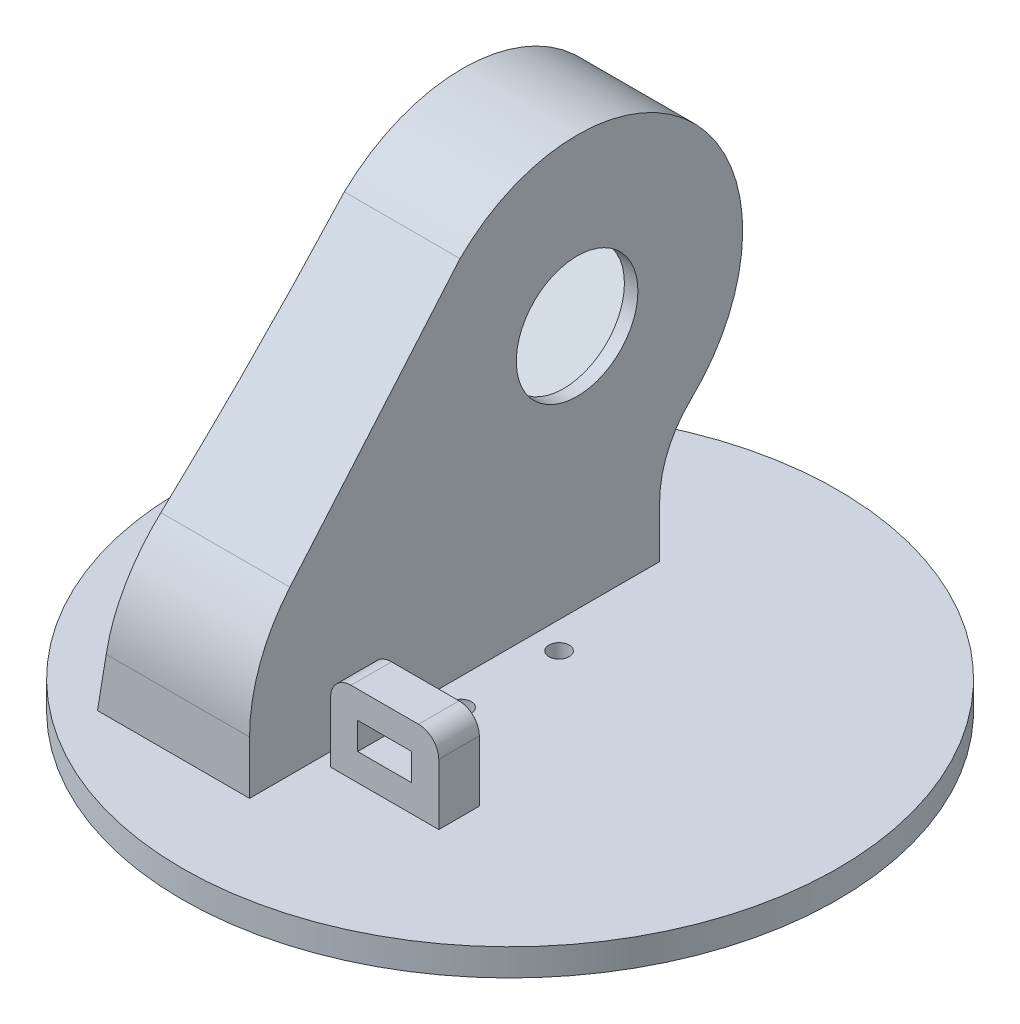
SolidWorks part; units mm, degrees
ref_plane "Front Plane" through (0, 0, 0) normal (0, 0, 1) x (1, 0, 0)
ref_plane "Top Plane" through (0, 0, 0) normal (0, 1, 0) x (1, 0, 0)
ref_plane "Right Plane" through (0, 0, 0) normal (1, 0, 0) x (0, 0, -1)
sketch "Sketch2" plane through (0, 0, 0) normal (0, 1, 0) x (1, 0, 0)
  circle A0 centre (0, 0) radius 48.5
  dimension "D1" = 97
extrude "Boss-Extrude1" add sketch "Sketch2" along normal blind 4
sketch "Sketch4" plane through (0, 0, 0) normal (0, -1, 0) x (1, 0, 0)
  circle A0 centre (0, 7.25) radius 1.5
  circle A1 centre (0, -7.25) radius 1.5
  dimension "D1" = 3
  dimension "D2" = 3
  dimension "D3" = 14.5
  dimension "D4" = 7.25
extrude "Cut-Extrude2" cut sketch "Sketch4" against normal through all
sketch "Sketch5" plane through (0, 0, 0) normal (0, -1, 0) x (1, 0, 0)
  circle A0 centre (0, 0) radius 3.75
  dimension "D1" = 7.5
extrude "Cut-Extrude3" cut sketch "Sketch5" against normal blind 1.5
ref_plane "Plane1" through (-4, 0, 0) normal (1, 0, 0) x (0, 0, -1)
sketch "Sketch7" plane through (-4, 0, 0) normal (1, 0, 0) x (0, 0, -1)
  line L0 (23.1299, 11.6445) -> (23.1299, 4)
  line L5 (48.5, 4) -> (-48.5, 4) construction
  line L6 (-27.2273, 29.5362) -> (-1.2843, 55.4793)
  line L7 (-43.5609, 4) -> (23.1299, 4)
  line L11 (-34.5496, 4) -> (-34.5496, 11.8586)
  arc A4 (28.7298, 24.692) -> (-1.2843, 55.4793) centre (13.9185, 40.2765) ccw
  arc A5 (28.7298, 24.692) -> (23.1299, 11.6445) centre (41.1299, 11.6445) ccw
  arc A6 (-27.2273, 29.5362) -> (-34.5496, 11.8586) centre (-9.5496, 11.8586) ccw
  dimension "D1" = 25
  dimension "D4" = 43
  dimension "D3" = 18
  dimension "D5" = 45
extrude "Boss-Extrude2" add sketch "Sketch7" against normal blind 14
ref_plane "Plane2" through (-6, 0, 0) normal (1, 0, 0) x (0, 0, -1)
sketch "Sketch8" plane through (-6, 0, 0) normal (1, 0, 0) x (0, 0, -1)
  line L0 (-27.2273, 29.5362) -> (-1.2843, 55.4793) construction
  line L1 (-15.2496, 25.9576) -> (13.7417, 54.9489)
  line L2 (-15.2496, 25.9576) -> (-0.4004, 11.1083)
  line L3 (-0.4004, 11.1083) -> (28.591, 40.0997)
  line L4 (13.7417, 54.9489) -> (28.591, 40.0997)
  line L5 (-15.2496, 25.9576) -> (28.591, 40.0997) construction
  line L6 (-0.4004, 11.1083) -> (13.7417, 54.9489) construction
  point P0 (6.6707, 33.0286)
  point P11 (13.9185, 40.2765)
  dimension "D1" = 41
  dimension "D2" = 21
  dimension "D3" = 90
  dimension "D4" = 20.5
  dimension "D5" = 90
  dimension "D6" = 10.25
  dimension "D7" = 10.5
extrude "Cut-Extrude5" cut sketch "Sketch8" against normal up to next
sketch "Sketch9" plane through (-18, 0, 0) normal (-1, 0, 0) x (0, 0, 1)
  line L0 (-13.7417, 54.9489) -> (-28.591, 40.0997) construction
  line L3 (-21.1664, 47.5243) -> (-22.536, 48.894) construction
  circle A0 centre (-20.1057, 53.5347) radius 1.3
  circle A1 centre (-27.1768, 46.4637) radius 1.3
  circle A2 centre (6.7644, 12.5225) radius 1.3
  circle A3 centre (13.8354, 19.5936) radius 1.3
  dimension "D1" = 2.6
  dimension "D5" = 5
  dimension "D6" = 90
  dimension "D2" = 3.5
  dimension "D3" = 2
  dimension "D4" = 2
extrude "Cut-Extrude6" cut sketch "Sketch9" against normal blind 7.5
sketch "Sketch11" plane through (-4, 0, 0) normal (1, 0, 0) x (0, 0, -1)
  circle A0 centre (13.9185, 40.2765) radius 9
  dimension "D1" = 18
extrude "Cut-Extrude9" cut sketch "Sketch11" against normal up to next
sketch "Sketch17" plane through (-18, 0, 0) normal (-1, 0, 0) x (0, 0, 1)
  line L0 (29.3486, 31.6576) -> (3.4056, 57.6006)
  line L1 (-26.1299, 11.6445) -> (-26.1299, 1)
  line L2 (-26.1299, 1) -> (37.5496, 1)
  line L3 (37.5496, 1) -> (37.5496, 11.8586)
  line L4 (27.2273, 29.5362) -> (1.2843, 55.4793)
  line L5 (-23.1299, 11.6445) -> (-23.1299, 4)
  line L6 (-23.1299, 4) -> (34.5496, 4)
  line L7 (34.5496, 4) -> (34.5496, 11.8586)
  line L9 (-23.1299, 11.6445) -> (-23.1299, 4)
  line L10 (-23.1299, 4) -> (34.5496, 4)
  line L11 (34.5496, 4) -> (34.5496, 11.8586)
  line L12 (-26.1299, 4) -> (37.5496, 4)
  line L13 (48.5, 4) -> (-48.5, 4) construction
  line L14 (3.4056, 57.6006) -> (28.5745, 28.0776)
  line L15 (1.2843, 55.4793) -> (26.295, 26.1272)
  line L16 (31.5496, 11.8586) -> (31.5496, 4)
  line L18 (27.2273, 29.5362) -> (1.2843, 55.4793) construction
  arc A0 (3.4056, 57.6006) -> (-30.7965, 22.5174) centre (-13.9185, 40.2765) ccw
  arc A1 (-26.1299, 11.6445) -> (-30.7965, 22.5174) centre (-41.1299, 11.6445) ccw
  arc A2 (37.5496, 11.8586) -> (29.3486, 31.6576) centre (9.5496, 11.8586) ccw
  arc A3 (1.2843, 55.4793) -> (-28.7298, 24.692) centre (-13.9185, 40.2765) ccw
  arc A4 (-23.1299, 11.6445) -> (-28.7298, 24.692) centre (-41.1299, 11.6445) ccw
  arc A5 (34.5496, 11.8586) -> (27.2273, 29.5362) centre (9.5496, 11.8586) ccw
  arc A6 (1.2843, 55.4793) -> (-28.7298, 24.692) centre (-13.9185, 40.2765) ccw
  arc A7 (-23.1299, 11.6445) -> (-28.7298, 24.692) centre (-41.1299, 11.6445) ccw
  arc A8 (34.5496, 11.8586) -> (27.2273, 29.5362) centre (9.5496, 11.8586) ccw
  arc A9 (31.5496, 11.8586) -> (25.106, 27.4149) centre (9.5496, 11.8586) ccw
  line M16 (27.2273, 29.5362) -> (1.2843, 55.4793)
  arc M17 (1.2843, 55.4793) -> (-28.7298, 24.692) centre (-13.9185, 40.2765) ccw
  arc M18 (-28.7298, 24.692) -> (-23.1299, 11.6445) centre (-41.1299, 11.6445) cw
  line M19 (-23.1299, 11.6445) -> (-23.1299, 4)
  line M21 (34.5496, 4) -> (34.5496, 11.8586)
  arc M22 (34.5496, 11.8586) -> (27.2273, 29.5362) centre (9.5496, 11.8586) ccw
  dimension "D1" = 0
  dimension "D2" = 3
  dimension "D3" = 3
extrude "Boss-Extrude7" add sketch "Sketch17" along normal blind 9 and the other way up to surface (14 mm away) contours A9 L16 L12 L15 M21 M22 M16 | A1 L1 L12 L14 A0 M19 M18 M17 M16 M22 other way up to face at (-4, 40.2765, -22.9185)
sketch "Sketch25" plane through (-18, 0, 0) normal (-1, 0, 0) x (0, 0, 1)
  line L0 (-23.1299, 11.6445) -> (-23.1299, 4)
  line L1 (48.5, 4) -> (-48.5, 4) construction
  line L2 (-23.1299, 11.6445) -> (-23.1299, 4) construction
  line L3 (1.2843, 55.4793) -> (26.295, 26.1272) construction
  line L4 (31.5496, 4) -> (-23.1299, 4) construction
  line L5 (31.5496, 11.8586) -> (31.5496, 4) construction
  line L6 (31.5496, 4) -> (-23.1299, 4)
  line L7 (31.5496, 11.8586) -> (31.5496, 4)
  line L8 (1.2843, 55.4793) -> (26.295, 26.1272)
  arc A0 (-23.1299, 11.6445) -> (-28.7298, 24.692) centre (-41.1299, 11.6445) ccw construction
  arc A1 (1.2843, 55.4793) -> (-28.7298, 24.692) centre (-13.9185, 40.2765) ccw construction
  arc A2 (-23.1299, 11.6445) -> (-28.7298, 24.692) centre (-41.1299, 11.6445) ccw
  arc A3 (31.5496, 11.8586) -> (26.295, 26.1272) centre (9.5496, 11.8586) ccw construction
  arc A4 (31.5496, 11.8586) -> (26.295, 26.1272) centre (9.5496, 11.8586) ccw
  spline S0 degree 3 poles (-28.7298, 24.692) (-21.9549, 18.2532) (-19.0941, 12.798) (-15.1299, 4) knots 0 0 0 0 1 1 1 1
  spline S1 degree 2 poles (11.7516, 43.195) (26.5513, 25.8264) (25.5496, 4) knots 0 0 0 1 1 1
  dimension "D2" = 8
  dimension "D1" = 6
extrude "Boss-Extrude10" add sketch "Sketch25" along normal up to surface (9 mm away) contours S0 L6 L0 A2 | A4 S1 A2 S0 L8 up to face at (-27, 22.2911, 0.3951)
sketch "Sketch26" plane through (0, 0, 0) normal (0, 0, 1) x (1, 0, 0)
  line L0 (-4, 64.7765) -> (-27, 64.7765) construction
  line L1 (-27, 4) -> (-4, 4) construction
  line L2 (-27, 4) -> (-27, 11.8586) construction
  line L3 (-26, 64.7765) -> (-27, 64.7765)
  line L4 (-27, 64.7765) -> (-27, 4)
  line L5 (-27, 4) -> (-23, 4)
  spline S0 degree 2 poles (-26, 64.7765) (-24.7724, 34.3751) (-23, 4) knots 0 0 0 1 1 1
  dimension "D1" = 1
  dimension "D2" = 4
  dimension "D3" = 2
extrude "Cut-Extrude15" [suppressed] cut sketch "Sketch26" against normal through all both and the other way through all contours L4 L5 S0 L3
sketch "Sketch27" plane through (0, 4, 0) normal (0, 1, 0) x (1, 0, 0)
  line L1 (-2, -18.5496) -> (14, -18.5496)
  line L2 (-2, -18.5496) -> (-2, -24.5496)
  line L3 (-2, -24.5496) -> (14, -24.5496)
  line L4 (14, -18.5496) -> (14, -24.5496)
  line L5 (-27, -34.5496) -> (-4, -34.5496) construction
  line L6 (-4, -34.5496) -> (-4, 26.1299) construction
  dimension "D1" = 10
  dimension "D2" = 6
  dimension "D3" = 16
  dimension "D4" = 2
extrude "Boss-Extrude11" add sketch "Sketch27" along normal blind 12
fillet "Fillet6" radius 3 2 edges at (14, 16, 21.5496) (-2, 16, 21.5496)
sketch "Sketch28" plane through (0, 0, 24.5496) normal (0, 0, 1) x (1, 0, 0)
  line L8 (10, 12) -> (2, 12)
  line L9 (2, 12) -> (2, 8)
  line L10 (2, 8) -> (10, 8)
  line L11 (10, 8) -> (10, 12)
  line L12 (10, 12) -> (2, 12)
  line L13 (2, 12) -> (2, 8)
  line L14 (2, 8) -> (10, 8)
  line L15 (10, 8) -> (10, 12)
  dimension "D1" = 4
extrude "Cut-Extrude16" cut sketch "Sketch28" against normal up to next
sketch "Sketch29" plane through (0, 0, 0) normal (0, 0, 1) x (1, 0, 0)
  line L0 (-4, 64.7765) -> (-27, 64.7765) construction
  line L1 (-27, 4) -> (-4, 4) construction
  line L2 (-21, 64.7765) -> (-27, 64.7765)
  line L3 (-27, 64.7765) -> (-27, 4)
  line L4 (-27, 4) -> (-26.5, 4)
  line L5 (48.5, 4) -> (-48.5, 4) construction
  spline S0 degree 2 poles (-21, 64.7765) (-21.2205, 34.1409) (-26.5, 4) knots 0 0 0 1 1 1
  dimension "D1" = 6
  dimension "D2" = 4
  dimension "D3" = 0.5
  dimension "D4" = 25
extrude "Cut-Extrude17" cut sketch "Sketch29" against normal through all both and the other way through all
